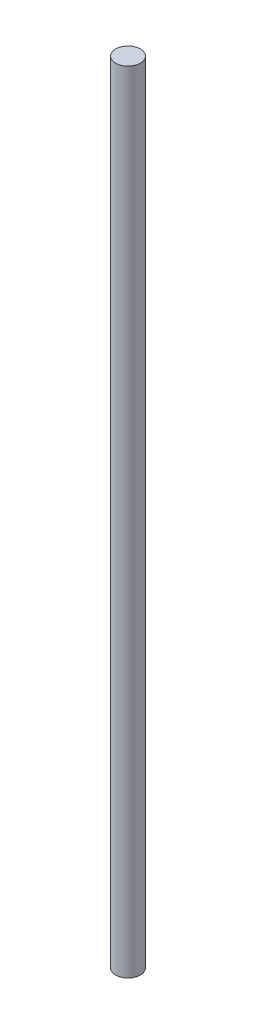
SolidWorks part; units mm, degrees
ref_plane "Front Plane" through (0, 0, 0) normal (0, 0, 1) x (1, 0, 0)
ref_plane "Top Plane" through (0, 0, 0) normal (0, 1, 0) x (1, 0, 0)
ref_plane "Right Plane" through (0, 0, 0) normal (1, 0, 0) x (0, 0, -1)
sketch "Sketch1" plane through (0, 0, 0) normal (0, 1, 0) x (1, 0, 0)
  circle A0 centre (0, 0) radius 3.175
  dimension "D1" = 6.35
extrude "Boss-Extrude1" add sketch "Sketch1" along normal blind 203.2
